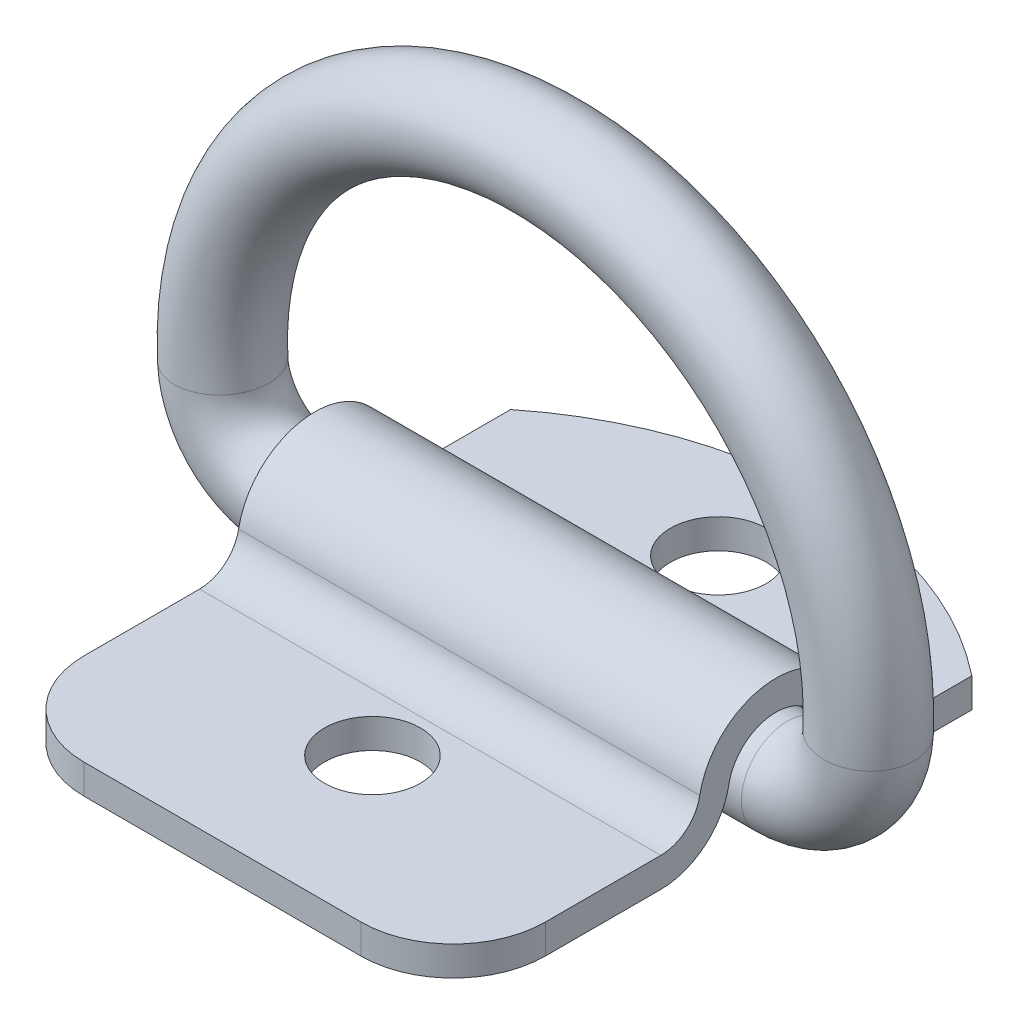
SolidWorks part; units mm, degrees
ref_plane "Front Plane" through (0, 0, 0) normal (0, 0, 1) x (1, 0, 0)
ref_plane "Top Plane" through (0, 0, 0) normal (0, 1, 0) x (1, 0, 0)
ref_plane "Right Plane" through (0, 0, 0) normal (1, 0, 0) x (0, 0, -1)
sketch "Sketch1" plane through (0, 0, 0) normal (0, 0, 1) x (1, 0, 0)
  line L0 (-19.068, 6.332) -> (19.068, 6.332) construction
  line L1 (0, 0) -> (0, 31.75) construction
  line L6 (16.6687, 3.175) -> (-16.6687, 3.175) construction
  line L7 (16.6687, -3.175) -> (-16.6687, -3.175) construction
  line L8 (0, 3.175) -> (0, -3.175) construction
  line L12 (-16.6687, 0) -> (16.6687, 0)
  arc A0 (25.3906, 5.1504) -> (-25.3906, 5.1504) centre (0, 6.332) ccw construction
  arc A1 (19.0474, 5.4456) -> (-19.0474, 5.4456) centre (0, 6.332) ccw construction
  circle A2 centre (0, 28.575) radius 3.175 construction
  circle A3 centre (0, 0) radius 3.175 construction
  arc A4 (22.219, 5.298) -> (-22.219, 5.298) centre (0, 6.332) ccw
  arc A5 (-16.6687, 0) -> (-22.219, 5.298) centre (-16.6687, 5.5562) cw
  arc A6 (16.6687, -3.175) -> (25.3906, 5.1504) centre (16.6687, 5.5562) ccw construction
  arc A7 (-16.6687, 3.175) -> (-19.0474, 5.4456) centre (-16.6687, 5.5562) cw construction
  arc A8 (-16.6687, -3.175) -> (-25.3906, 5.1504) centre (-16.6687, 5.5562) cw construction
  arc A9 (16.6687, 0) -> (22.219, 5.298) centre (16.6687, 5.5562) ccw
  arc A10 (16.6687, 3.175) -> (19.0474, 5.4456) centre (16.6687, 5.5562) ccw construction
  dimension "C" = 6.35
  dimension "D1" = 5.5562
  dimension "A" = 38.1
  dimension "B" = 34.925
sketch "Sketch2" plane through (0, 0, 0) normal (1, 0, 0) x (0, 0, -1)
  circle A0 centre (0, 0) radius 3.175
sweep "Sweep1" add profiles "Sketch2" path "Sketch1"
sketch "Sketch3" plane through (0, 0, 0) normal (1, 0, 0) x (0, 0, -1)
  line L0 (-22.225, -3.302) -> (19.05, -3.302) construction
  line L1 (-22.225, -3.302) -> (-22.225, -1.27)
  line L2 (-22.225, -1.27) -> (19.05, -1.27) construction
  line L3 (0, 0) -> (0, -3.302) construction
  line L4 (19.05, -3.302) -> (19.05, -1.27)
  line L5 (-22.225, -3.302) -> (-7.9311, -3.302)
  line L6 (-22.225, -1.27) -> (-7.9311, -1.27)
  line L7 (-11.9062, -3.302) -> (-11.9062, -1.27) construction
  line L8 (19.05, -3.302) -> (7.9311, -3.302)
  line L9 (19.05, -1.27) -> (7.9311, -1.27)
  arc A0 (-7.9311, -3.302) -> (-3.2474, 0.598) centre (-7.9311, 1.4605) ccw
  arc A1 (-3.2474, 0.598) -> (3.2474, 0.598) centre (0, 0) cw
  arc A2 (-7.9311, -1.27) -> (-5.2458, 0.966) centre (-7.9311, 1.4605) ccw
  arc A3 (-5.2458, 0.966) -> (5.2458, 0.966) centre (0, 0) cw
  arc A4 (7.9311, -1.27) -> (5.2458, 0.966) centre (7.9311, 1.4605) cw
  arc A5 (7.9311, -3.302) -> (3.2474, 0.598) centre (7.9311, 1.4605) cw
  circle A6 centre (0, 0) radius 3.302 construction
  dimension "D1" = 23.8125
  dimension "D6" = 8.636
  dimension "D4" = 6.604
  dimension "D5" = 4.7625
  dimension "D2" = 2.032
  dimension "D3" = 41.275
  dimension "D7" = 22.225
  dimension "D8" = 19.05
extrude "Boss-Extrude1" add sketch "Sketch3" along normal mid plane 31.75 separate body
sketch "Sketch4" plane through (0, -3.302, 0) normal (0, -1, 0) x (1, 0, 0)
  line L0 (15.875, -19.05) -> (-15.875, -19.05) construction
  line L1 (-15.875, 15.875) -> (-15.875, 22.225)
  line L2 (-15.875, 22.225) -> (-9.525, 22.225)
  line L3 (15.875, 22.225) -> (9.525, 22.225)
  line L4 (15.875, 15.875) -> (15.875, 22.225)
  line L5 (0, -6.35) -> (0, 0) construction
  line L7 (-15.875, 0) -> (15.875, 0) construction
  line L8 (15.875, -19.05) -> (15.875, -13.4779)
  line L9 (15.875, -20.32) -> (15.875, -19.05)
  line L10 (-15.875, -20.32) -> (15.875, -20.32)
  line L11 (-15.875, -19.05) -> (-15.875, -20.32)
  line L12 (-15.875, -13.4779) -> (-15.875, -19.05)
  arc A0 (-9.525, 22.225) -> (-15.875, 15.875) centre (-9.525, 15.875) ccw
  circle A1 centre (0, 11.9062) radius 3.302
  circle A2 centre (0, -11.9062) radius 3.302
  arc A3 (15.875, -13.4779) -> (-15.875, -13.4779) centre (0, 6.35) cw
  arc A4 (9.525, 22.225) -> (15.875, 15.875) centre (9.525, 15.875) cw
  dimension "D1" = 25.4
  dimension "D3" = 6.604
  dimension "D4" = 1.27
  dimension "D5" = 6.35
  dimension "D2" = 5.5721
extrude "Cut-Extrude1" cut sketch "Sketch4" against normal through all
